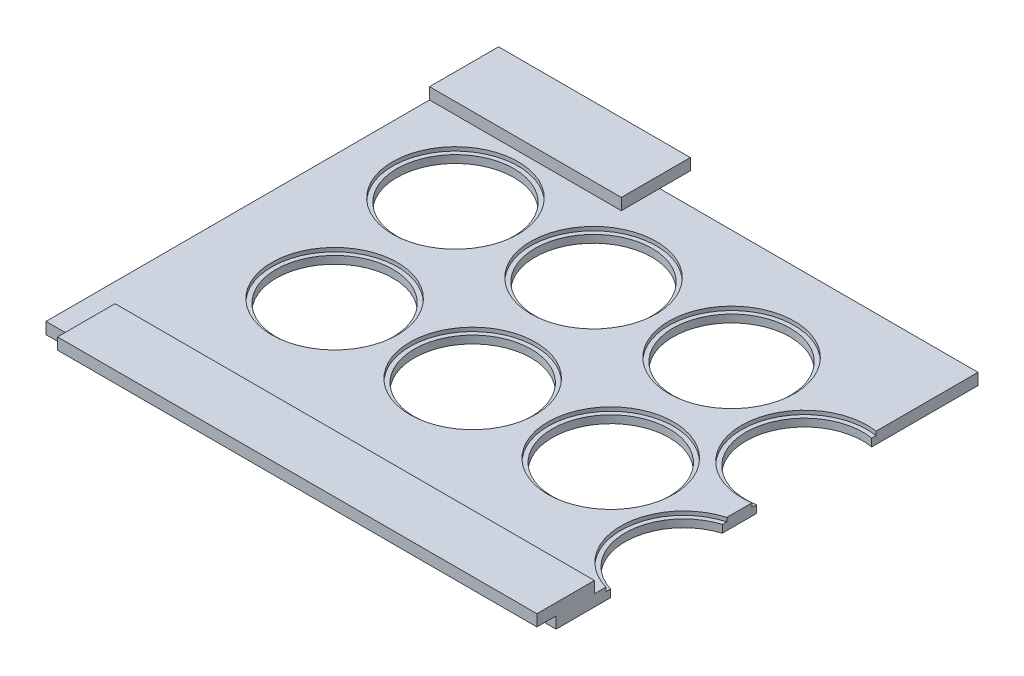
SolidWorks part; units mm, degrees
ref_plane "Front Plane" through (0, 0, 0) normal (0, 0, 1) x (1, 0, 0)
ref_plane "Top Plane" through (0, 0, 0) normal (0, 1, 0) x (1, 0, 0)
ref_plane "Right Plane" through (0, 0, 0) normal (1, 0, 0) x (0, 0, -1)
sketch "Sketch1" plane through (0, 0, 0) normal (0, 1, 0) x (1, 0, 0)
  line L1 (0, 0) -> (133, 0)
  line L2 (0, 0) -> (0, 110)
  line L3 (0, 110) -> (133, 110)
  line L4 (133, 0) -> (133, 110)
  dimension "D1" = 110
  dimension "D2" = 133
extrude "Boss-Extrude1" add sketch "Sketch1" along normal blind 3
sketch "Sketch2" plane through (0, 3, 0) normal (0, 1, 0) x (1, 0, 0)
  line L1 (0, 118) -> (50, 118)
  line L2 (0, 118) -> (0, 100)
  line L3 (0, 100) -> (50, 100)
  line L4 (50, 118) -> (50, 100)
  line L6 (133, 110) -> (0, 110) construction
  dimension "D1" = 10
  dimension "D2" = 50
  dimension "D3" = 18
extrude "Boss-Extrude2" add sketch "Sketch2" along normal blind 3
sketch "Sketch3" plane through (0, 3, 0) normal (0, 1, 0) x (1, 0, 0)
  line L0 (0, 100) -> (0, 0) construction
  line L1 (133, -5) -> (8, -5)
  line L2 (133, -5) -> (133, 10)
  line L3 (133, 10) -> (8, 10)
  line L4 (8, -5) -> (8, 10)
  line L6 (0, 0) -> (133, 0) construction
  line L7 (133, 0) -> (133, 110) construction
  dimension "D1" = 8
  dimension "D2" = 10
  dimension "D3" = 15
extrude "Boss-Extrude3" add sketch "Sketch3" along normal blind 3
sketch "Sketch4" plane through (0, 0, 0) normal (0, -1, 0) x (1, 0, 0)
  line L0 (133, -110) -> (0, -110) construction
  line L1 (0, -110) -> (0, 0) construction
  circle A0 centre (25.5, -81.25) radius 15.25
  circle A1 centre (32.5, -42.75) radius 15.25
  circle A2 centre (61.5, -81.25) radius 15.25
  circle A3 centre (97.5, -81.25) radius 15.25
  circle A4 centre (130.5, -67.25) radius 15.25
  circle A5 centre (68.5, -42.75) radius 15.25
  circle A6 centre (104.5, -42.75) radius 15.25
  circle A7 centre (137.5, -28.75) radius 15.25
  dimension "D3" = 30.5
  dimension "D9" = 14
  dimension "D1" = 28.75
  dimension "D2" = 25.5
  dimension "D4" = 36
  dimension "D5" = 7
  dimension "D6" = 36
  dimension "D7" = 36
  dimension "D8" = 36
  dimension "D10" = 33
  dimension "D11" = 14
  dimension "D12" = 33
  dimension "D13" = 38.5
extrude "Cut-Extrude1" cut sketch "Sketch4" against normal up to surface (3 mm away) up to face at (47.75, 3, -55)
sketch "Sketch5" plane through (0, 3, 0) normal (0, 1, 0) x (1, 0, 0)
  line L0 (8, 5) -> (8, 94.8693) construction
  line L1 (8, 10) -> (8, 0) construction
  circle A0 centre (25.5, 81.25) radius 16.375
  circle A1 centre (61.5, 81.25) radius 16.375
  circle A2 centre (97.5, 81.25) radius 16.375
  circle A3 centre (32.5, 42.75) radius 16.375
  circle A4 centre (68.5, 42.75) radius 16.375
  circle A5 centre (104.5, 42.75) radius 16.375
  circle A6 centre (130.5, 67.25) radius 16.375
  circle A7 centre (137.5, 28.75) radius 16.375
  dimension "D1" = 32.75
extrude "Cut-Extrude2" cut sketch "Sketch5" against normal blind 1
